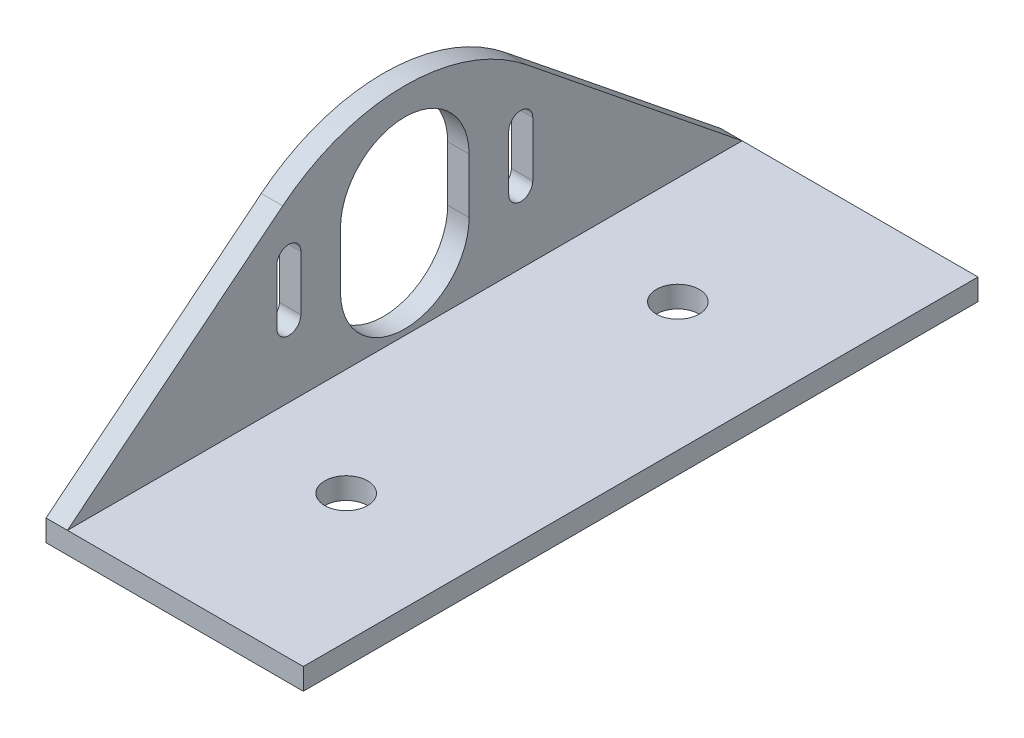
SolidWorks part; units mm, degrees
material "6061-T6 (SS)"
ref_plane "Front Plane" through (0, 0, 0) normal (0, 0, 1) x (1, 0, 0)
ref_plane "Top Plane" through (0, 0, 0) normal (0, 1, 0) x (1, 0, 0)
ref_plane "Right Plane" through (0, 0, 0) normal (1, 0, 0) x (0, 0, -1)
sketch "Sketch1" plane through (0, 0, 0) normal (0, 1, 0) x (1, 0, 0)
  line L1 (-66.675, 25.4) -> (66.675, 25.4)
  line L2 (-66.675, 25.4) -> (-66.675, -25.4)
  line L3 (-66.675, -25.4) -> (66.675, -25.4)
  line L4 (66.675, 25.4) -> (66.675, -25.4)
  line L5 (-66.675, 25.4) -> (66.675, -25.4) construction
  line L6 (-66.675, -25.4) -> (66.675, 25.4) construction
  point P0 (0, 0)
  dimension "D1" = 133.35
  dimension "D2" = 50.8
extrude "Boss-Extrude1" add sketch "Sketch1" along normal blind 3.175
sketch "Sketch4" plane through (0, 0, 25.4) normal (0, 0, 1) x (1, 0, 0)
  line L0 (-66.675, 0) -> (66.675, 0) construction
  line L1 (38.1, 3.175) -> (-38.1, 3.175)
  line L2 (38.1, 3.175) -> (38.1, 0)
  line L3 (38.1, 0) -> (-38.1, 0)
  line L4 (-38.1, 3.175) -> (-38.1, 0)
  line L5 (38.1, 3.175) -> (-38.1, 0) construction
  line L6 (38.1, 0) -> (-38.1, 3.175) construction
  line L7 (-66.675, 3.175) -> (0, 1.5875) construction
  line L8 (0, 1.5875) -> (66.675, 3.175) construction
  line L9 (-66.675, 3.175) -> (66.675, 3.175) construction
  point P0 (0, 1.5875)
  dimension "D1" = 76.2
extrude "Boss-Extrude2" add sketch "Sketch4" along normal blind 147.32
sketch "Sketch3" plane through (0, 3.175, 0) normal (0, 1, 0) x (1, 0, 0)
  line L0 (0, 0) -> (0, -49.1067) construction
  line L1 (0, -49.1067) -> (0, -98.2133) construction
  line L2 (0, -98.2133) -> (0, -147.32) construction
  line L3 (38.1, -172.72) -> (-38.1, -172.72) construction
  circle A0 centre (0, 0) radius 3.175
  circle A1 centre (0, -49.1067) radius 3.175
  circle A2 centre (0, -98.2133) radius 3.175
  circle A3 centre (0, -147.32) radius 3.175
  dimension "D1" = 6.35
  dimension "D2" = 25.4
extrude "Cut-Extrude2" cut sketch "Sketch3" against normal through all
sketch "Sketch5" plane through (0, 3.175, 0) normal (0, 1, 0) x (1, 0, 0)
  line L0 (-66.675, 25.4) -> (-66.675, -25.4) construction
  line L1 (66.675, 25.4) -> (-66.675, 25.4)
  line L2 (66.675, 25.4) -> (66.675, -63.5)
  line L3 (66.675, -63.5) -> (-66.675, -63.5)
  line L4 (-66.675, 25.4) -> (-66.675, -63.5)
  dimension "D1" = 88.9
extrude "Cut-Extrude3" cut sketch "Sketch5" against normal through all
sketch "Sketch7" plane through (0, 3.175, 0) normal (0, 1, 0) x (1, 0, 0)
  line L0 (38.1, -172.72) -> (-38.1, -172.72) construction
  line L1 (-38.1, -63.5) -> (-15.875, -63.5)
  line L2 (-38.1, -63.5) -> (-38.1, -172.72)
  line L3 (-38.1, -172.72) -> (-15.875, -172.72)
  line L4 (-15.875, -63.5) -> (-15.875, -172.72)
  dimension "D1" = 22.225
extrude "Cut-Extrude4" cut sketch "Sketch7" against normal through all
sketch "Sketch8" plane through (0, 3.175, 0) normal (0, 1, 0) x (1, 0, 0)
  line L2 (-15.875, -172.72) -> (31.75, -172.72)
  line L3 (-15.875, -172.72) -> (-15.875, -72.8133)
  line L4 (-15.875, -72.8133) -> (31.75, -72.8133)
  line L6 (31.75, -172.72) -> (31.75, -72.8133)
  line L7 (38.1, -172.72) -> (38.1, -63.5) construction
  circle A2 centre (0, -98.2133) radius 3.175 construction
  dimension "D1" = 25.4
  dimension "D2" = 6.35
extrude "Cut-Extrude5" cut sketch "Sketch8" against normal through all flip side to cut
sketch "Sketch9" plane through (-15.875, 0, 0) normal (-1, 0, 0) x (0, 0, 1)
  line L0 (172.72, 3.175) -> (140.8474, 28.8498)
  line L1 (72.8133, 3.175) -> (104.6859, 28.8498)
  line L2 (172.72, 0) -> (172.72, 3.175) construction
  line L3 (172.72, 0) -> (72.8133, 0) construction
  line L4 (72.8133, 0) -> (72.8133, 3.175) construction
  line L5 (172.72, 0) -> (172.72, 3.175)
  line L6 (172.72, 0) -> (72.8133, 0)
  line L7 (72.8133, 0) -> (72.8133, 3.175)
  arc A0 (140.8474, 28.8498) -> (104.6859, 28.8498) centre (122.7667, 6.4045) ccw
  point P7 (122.7667, 46.6592)
  point P8 (122.7667, 6.4045)
extrude "Boss-Extrude4" add sketch "Sketch9" along normal blind 3.175 contours L0 A0 L1 L7 L6 L5
sketch "Sketch10" plane through (0, 3.175, 0) normal (0, 1, 0) x (1, 0, 0)
  line L1 (31.75, -172.72) -> (19.05, -172.72)
  line L2 (31.75, -172.72) -> (31.75, -72.8133)
  line L3 (31.75, -72.8133) -> (19.05, -72.8133)
  line L4 (19.05, -172.72) -> (19.05, -72.8133)
  dimension "D1" = 12.7
extrude "Cut-Extrude6" cut sketch "Sketch10" against normal through all
sketch "Sketch11" plane through (-19.05, 0, 0) normal (-1, 0, 0) x (0, 0, 1)
  line L0 (122.7667, 21.6805) -> (122.7667, 13.546) construction
  line L1 (132.2917, 21.6805) -> (132.2917, 13.546)
  line L2 (113.2417, 21.6805) -> (113.2417, 13.546)
  line L3 (139.9384, 21.6805) -> (139.9384, 13.546) construction
  line L4 (141.7164, 21.6805) -> (141.7164, 13.546)
  line L5 (138.1604, 21.6805) -> (138.1604, 13.546)
  line L6 (105.5949, 21.6805) -> (105.5949, 13.546) construction
  line L7 (107.3729, 21.6805) -> (107.3729, 13.546)
  line L8 (103.8169, 21.6805) -> (103.8169, 13.546)
  line L9 (122.7667, 35.2265) -> (122.7667, 21.6805) construction
  line L10 (122.7667, 13.546) -> (122.7667, 0) construction
  line L11 (172.72, 0) -> (72.8133, 0) construction
  line L12 (139.9384, 17.6132) -> (105.5949, 17.6132) construction
  arc A0 (132.2917, 21.6805) -> (113.2417, 21.6805) centre (122.7667, 21.6805) ccw
  arc A1 (113.2417, 13.546) -> (132.2917, 13.546) centre (122.7667, 13.546) ccw
  arc A2 (141.7164, 21.6805) -> (138.1604, 21.6805) centre (139.9384, 21.6805) ccw
  arc A3 (138.1604, 13.546) -> (141.7164, 13.546) centre (139.9384, 13.546) ccw
  arc A4 (107.3729, 21.6805) -> (103.8169, 21.6805) centre (105.5949, 21.6805) ccw
  arc A5 (103.8169, 13.546) -> (107.3729, 13.546) centre (105.5949, 13.546) ccw
  arc A7 (140.8474, 28.8498) -> (104.6859, 28.8498) centre (122.7667, 6.4045) ccw construction
  point P3 (122.7667, 17.6132)
  point P8 (139.9384, 17.6132)
  point P15 (105.5949, 17.6132)
  point P31 (105.5949, 17.6132)
  point P32 (105.5949, 13.546)
  point P33 (105.5949, 21.6805)
  point P35 (105.5949, 13.546)
  point P36 (103.8169, 13.546)
  point P39 (122.7667, 17.6132)
  point P42 (105.5949, 21.6805)
  point P43 (105.5949, 21.6805)
  point P44 (139.9384, 21.6805)
  point P45 (139.9384, 21.6805)
  dimension "D3" = 22.352
  dimension "D1" = 19.05
  dimension "D2" = 3.556
extrude "Cut-Extrude7" cut sketch "Sketch11" against normal through all
